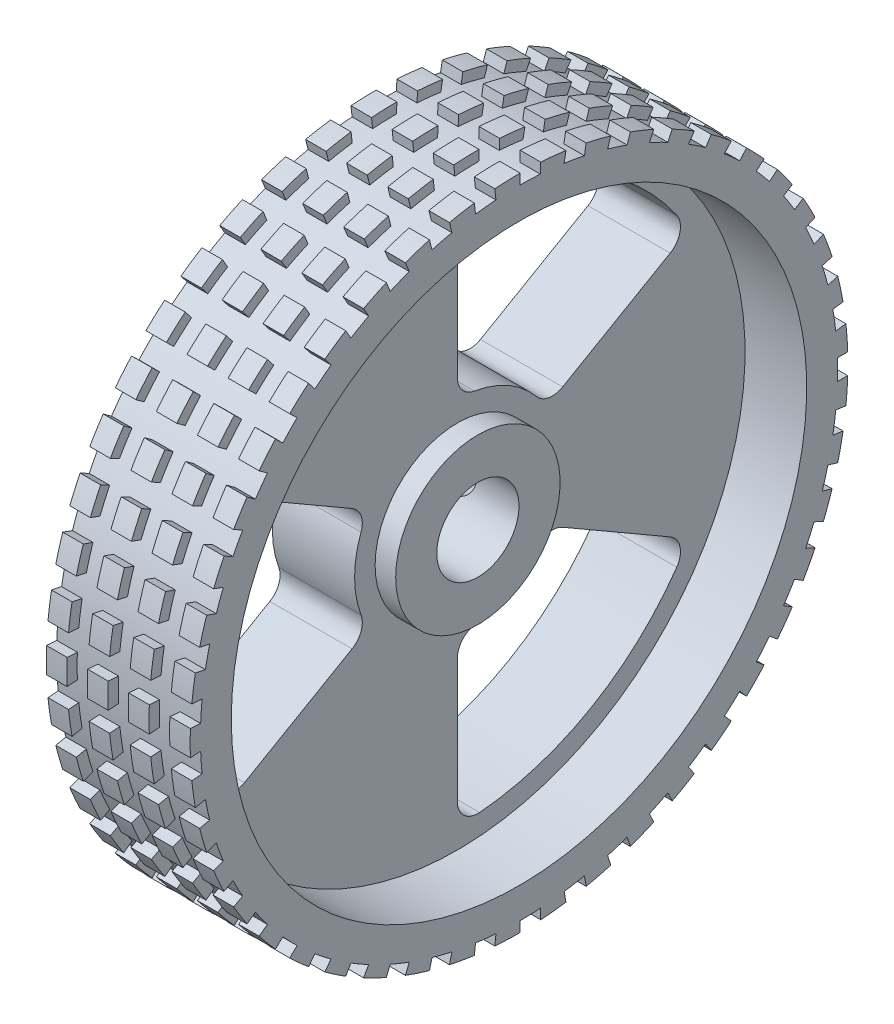
SolidWorks part; units mm, degrees
ref_plane "Front Plane" through (0, 0, 0) normal (0, 0, 1) x (1, 0, 0)
ref_plane "Top Plane" through (0, 0, 0) normal (0, 1, 0) x (1, 0, 0)
ref_plane "Right Plane" through (0, 0, 0) normal (1, 0, 0) x (0, 0, -1)
sketch "Sketch1" plane through (0, 0, 0) normal (0, 0, 1) x (1, 0, 0)
  line L0 (0, 0) -> (3.8986, 0) construction
  line L1 (0, 0) -> (0, 16)
  line L2 (0, 16) -> (7, 16)
  line L3 (7, 16) -> (7, 14)
  line L4 (7, 14) -> (4, 14)
  line L5 (4, 14) -> (4, 4)
  line L6 (4, 4) -> (5, 4)
  line L7 (5, 4) -> (5, 2)
  line L8 (5, 2) -> (0, 2)
  dimension "D1" = 32
  dimension "D2" = 7
  dimension "D3" = 28
  dimension "D4" = 5
  dimension "D5" = 8
  dimension "D6" = 4
  dimension "D7" = 4
revolve "Revolve1" add sketch "Sketch1" angle 360 about L0
sketch "Sketch3" plane through (0, 0, 0) normal (0, 1, 0) x (1, 0, 0)
  line L0 (2, 0) -> (2, 16) construction
  line L1 (7, 16) -> (0, 16) construction
  line L2 (2, 16) -> (3.5, 16)
  line L3 (3.5, 16) -> (3.5, 11.5)
  line L4 (3.5, 11.5) -> (2.9, 11.5)
  line L5 (2.9, 11.5) -> (2.9, 0)
  line L6 (2.9, 0) -> (2, 0)
  line L7 (0, 16) -> (0, -16) construction
  line L8 (2, 0) -> (2, 16)
  line L9 (2, 16) -> (2, 0)
  line L10 (2, 0) -> (2, 14.2458) construction
  line L11 (0, 0) -> (2.9, 0) construction
  dimension "D1" = 3
  dimension "D2" = 1.8
  dimension "D3" = 4.5
  dimension "D4" = 2
revolve "Cut-Revolve1" cut sketch "Sketch3" angle 360 about L0
sketch "Sketch4" plane through (4, 0, 0) normal (1, 0, 0) x (0, 0, -1)
  line L0 (0, 0) -> (3.7674, 6.5253) construction
  line L1 (0, 13) -> (0, 5)
  line L2 (11.2583, 6.5) -> (4.3301, 2.5)
  line L3 (0, 0) -> (11.324, 0) construction
  arc A0 (0, 5) -> (4.3301, 2.5) centre (0, 0) cw
  arc A1 (0, 13) -> (11.2583, 6.5) centre (0, 0) cw
  dimension "D1" = 5
  dimension "D2" = 13
  dimension "D3" = 60
  dimension "D4" = 60
extrude "Cut-Extrude1" cut sketch "Sketch4" against normal through all
fillet "Fillet1" radius 1 1 edges at (2, 2.5, -4.3301)
fillet "Fillet2" radius 1 1 edges at (2, 5, 0)
fillet "Fillet3" radius 1 1 edges at (2, 6.5, -11.2583)
fillet "Fillet4" radius 1 1 edges at (2, 13, 0)
pattern_circular "CirPattern1" count 3 every 120 about axis through (0, 0, 0) along (1, 0, 0) of "Cut-Extrude1", "Fillet1", "Fillet2", "Fillet3", "Fillet4"
sketch "Sketch5" plane through (0, 0, 0) normal (0, 0, 1) x (1, 0, 0)
  line L0 (7, 16) -> (0, 16) construction
  line L1 (5, 16) -> (6, 16)
  line L2 (5, 16) -> (5, 15.5)
  line L3 (5, 15.5) -> (6, 15.5)
  line L4 (6, 16) -> (6, 15.5)
  line L5 (7, -16) -> (7, 16) construction
  line L6 (0, 0) -> (17.8848, 0) construction
  dimension "D1" = 0.5
  dimension "D2" = 1
  dimension "D3" = 1
revolve "Cut-Revolve2" cut sketch "Sketch5" angle 360 about L6
sketch "Sketch6" plane through (7, 0, 0) normal (1, 0, 0) x (0, 0, -1)
  line L0 (0, 0) -> (25.9892, 0) construction
  line L5 (0, 0) -> (0, -1.1554) construction
  line L6 (15.9922, 0.5) -> (15.4919, 0.5)
  line L7 (15.9922, -0.5) -> (15.4919, -0.5)
  arc A0 (15.9922, 0.5) -> (15.9922, -0.5) centre (0, 0) cw
  circle A1 centre (0, 0) radius 16 construction
  arc A2 (15.4919, 0.5) -> (15.4919, -0.5) centre (0, 0) cw
  dimension "D1" = 0.5
  dimension "D2" = 1
extrude "Cut-Extrude2" cut sketch "Sketch6" against normal through all
pattern_linear "LPattern1" count 3 spacing 2 along (-1, 0, 0) of "Cut-Revolve2"
pattern_circular "CirPattern2" count 45 every 8 about axis through (0, 0, 0) along (1, 0, 0) of "Cut-Extrude2"
